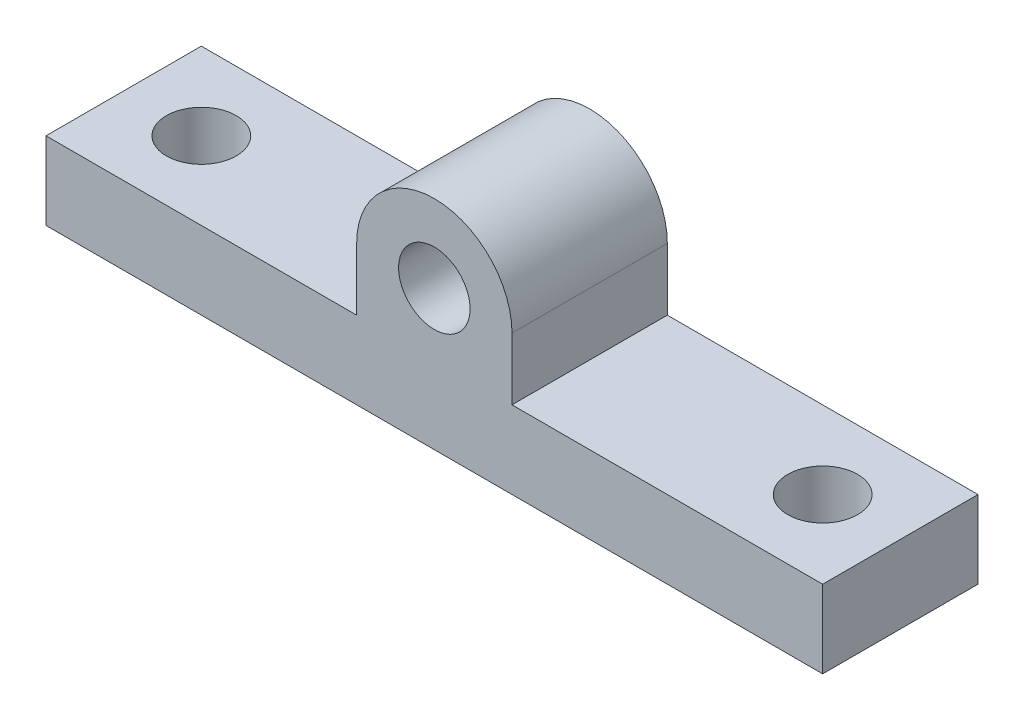
SolidWorks part; units mm, degrees
ref_plane "Front Plane" through (0, 0, 0) normal (0, 0, 1) x (1, 0, 0)
ref_plane "Top Plane" through (0, 0, 0) normal (0, 1, 0) x (1, 0, 0)
ref_plane "Right Plane" through (0, 0, 0) normal (1, 0, 0) x (0, 0, -1)
sketch "Sketch1" plane through (0, 0, 0) normal (0, 1, 0) x (1, 0, 0)
  line L0 (-25, -5) -> (25, -5)
  line L1 (-25, -5) -> (-25, 5)
  line L2 (25, -5) -> (25, 5)
  line L3 (-25, 5) -> (25, 5)
  line L4 (-25, 5) -> (25, -5) construction
  line L5 (25, -5) -> (25.6881, -6.3529) construction
  line L6 (20, 0) -> (0, 0) construction
  line L7 (0, 0) -> (-20, 0) construction
  circle A0 centre (-20, 0) radius 2.25
  circle A1 centre (20, 0) radius 2.25
  dimension "D3" = 4.5
  dimension "D4" = 40
  dimension "D1" = 50
  dimension "D2" = 10
extrude "Boss-Extrude1" add sketch "Sketch1" along normal blind 5
sketch "Sketch3" plane through (0, 0, 5) normal (0, 0, 1) x (1, 0, 0)
  line L0 (-5, 5) -> (-5, 9)
  line L1 (-25, 5) -> (25, 5) construction
  line L2 (5, 9) -> (5, 5)
  line L3 (5, 5) -> (-5, 5)
  line L4 (0, 9) -> (0, 0) construction
  arc A0 (-5, 9) -> (5, 9) centre (0, 9) cw
  circle A1 centre (0, 9) radius 2.3
  dimension "D1" = 4.6
  dimension "D2" = 10
  dimension "D3" = 9
extrude "Boss-Extrude2" add sketch "Sketch3" against normal up to surface (10 mm away) up to face at (0, 2.5, -5)
